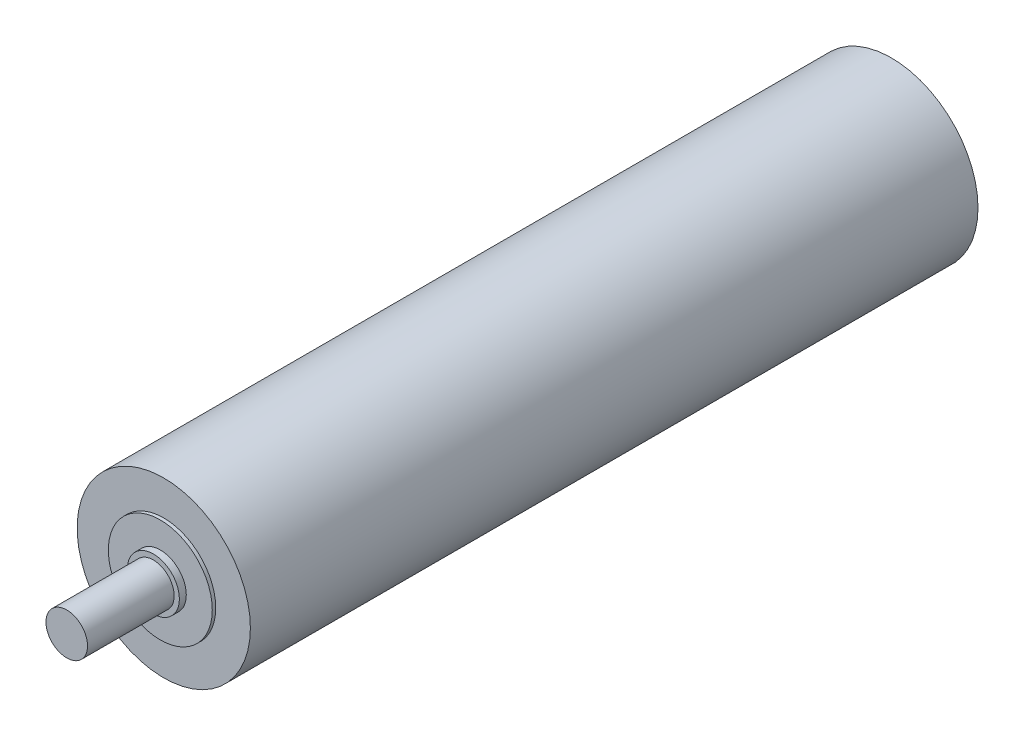
SolidWorks part; units mm, degrees
ref_plane "Front Plane" through (0, 0, 0) normal (0, 0, 1) x (1, 0, 0)
ref_plane "Top Plane" through (0, 0, 0) normal (0, 1, 0) x (1, 0, 0)
ref_plane "Right Plane" through (0, 0, 0) normal (1, 0, 0) x (0, 0, -1)
sketch "Sketch1" plane through (0, 0, 0) normal (0, 0, 1) x (1, 0, 0)
  circle A0 centre (0, 0) radius 25
  dimension "D1" = 50
extrude "Boss-Extrude2" add sketch "Sketch1" against normal blind 210
sketch "Sketch2" plane through (0, 0, 0) normal (0, 0, 1) x (1, 0, 0)
  circle A0 centre (0, 0) radius 15
  dimension "D1" = 30
extrude "Boss-Extrude3" add sketch "Sketch2" along normal blind 1
sketch "Sketch3" plane through (0, 0, 1) normal (0, 0, 1) x (1, 0, 0)
  circle A0 centre (0, 0) radius 7.5
  dimension "D1" = 15
extrude "Boss-Extrude4" add sketch "Sketch3" along normal blind 2
sketch "Sketch4" plane through (0, 0, 3) normal (0, 0, 1) x (1, 0, 0)
  circle A0 centre (0, 0) radius 6
  dimension "D1" = 12
extrude "Boss-Extrude5" add sketch "Sketch4" along normal blind 25
